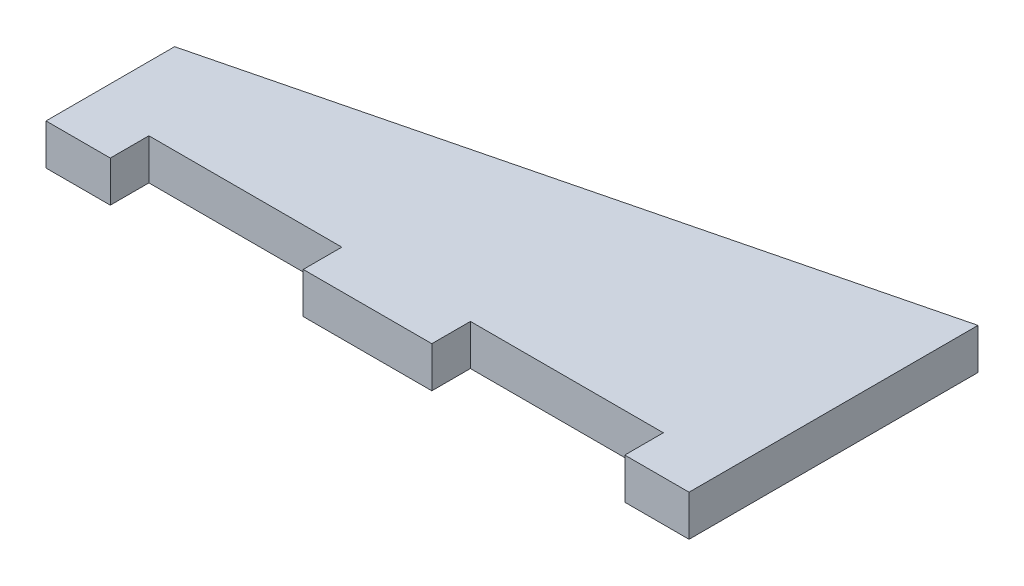
SolidWorks part; units mm, degrees
ref_plane "Front" through (0, 0, 0) normal (0, 0, 1) x (1, 0, 0)
ref_plane "Top" through (0, 0, 0) normal (0, 1, 0) x (1, 0, 0)
ref_plane "Right" through (0, 0, 0) normal (1, 0, 0) x (0, 0, -1)
sketch "Sketch1" plane through (0, 0, 0) normal (0, 1, 0) x (1, 0, 0)
  line L0 (0, 0) -> (10, 0)
  line L1 (10, 0) -> (10, 6)
  line L2 (10, 6) -> (40, 6)
  line L3 (40, 6) -> (40, 0)
  line L4 (40, 0) -> (60, 0)
  line L5 (60, 0) -> (60, 6)
  line L6 (60, 6) -> (90, 6)
  line L7 (90, 6) -> (90, 0)
  line L8 (90, 0) -> (100, 0)
  line L9 (100, 0) -> (100, 44.9328)
  line L10 (100, 44.9328) -> (0, 20)
  line L11 (0, 20) -> (0, 0)
  dimension "D1" = 100
  dimension "D2" = 104
  dimension "D3" = 10
  dimension "D4" = 20
  dimension "D5" = 30
  dimension "D6" = 30
  dimension "D7" = 6
  dimension "D8" = 6
  dimension "D9" = 20
extrude "Boss-Extrude1" add sketch "Sketch1" along normal blind 6.35
